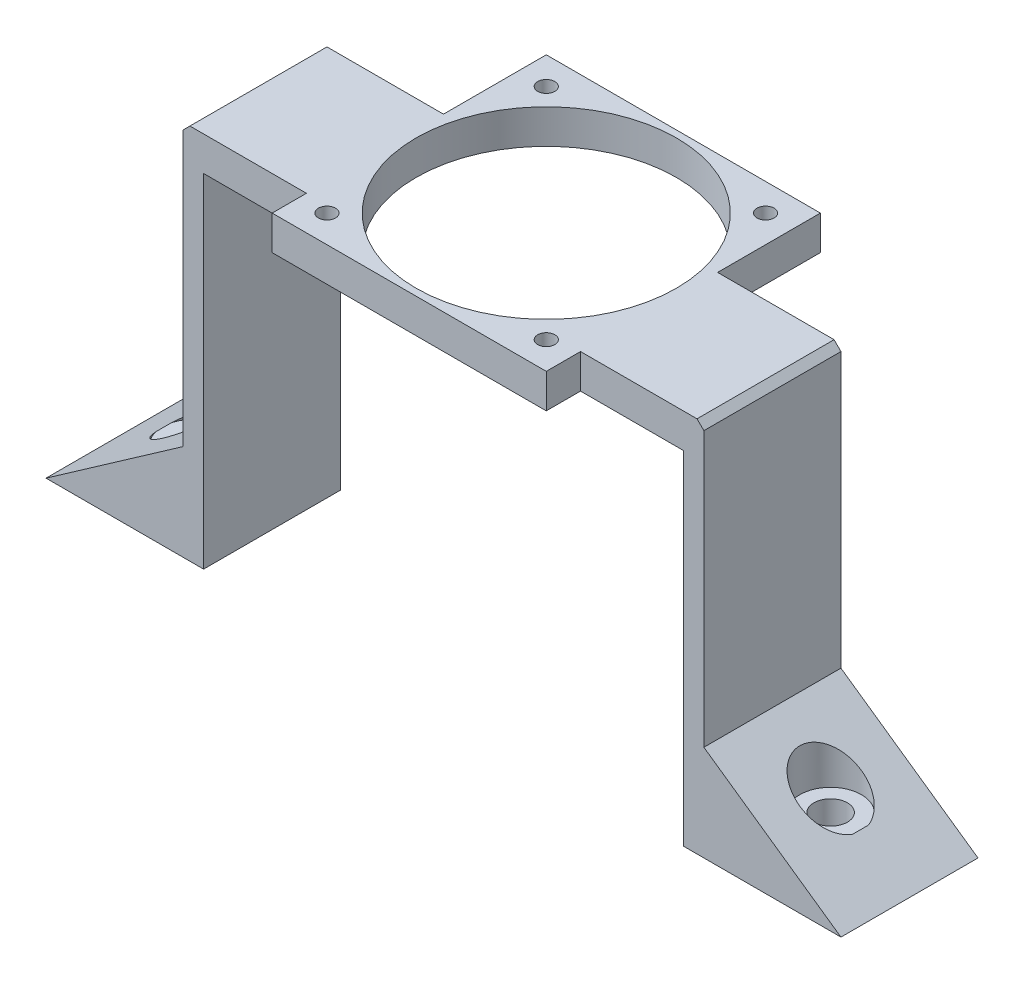
SolidWorks part; units mm, degrees
ref_plane "前视基准面" through (0, 0, 0) normal (0, 0, 1) x (1, 0, 0)
ref_plane "上视基准面" through (0, 0, 0) normal (0, 1, 0) x (1, 0, 0)
ref_plane "右视基准面" through (0, 0, 0) normal (1, 0, 0) x (0, 0, -1)
sketch "草图1" plane through (0, 0, 0) normal (0, 0, 1) x (1, 0, 0)
  line L0 (-33.5856, 27.9887) -> (-33.5856, -25.0113)
  line L1 (-30.5856, 24.9887) -> (39.4144, 24.9887)
  line L2 (-30.5856, 24.9887) -> (-30.5856, -25.0113)
  line L4 (39.4144, 24.9887) -> (39.4144, -25.0113)
  line L5 (-33.5856, 27.9887) -> (42.4144, 27.9887)
  line L6 (42.4144, 27.9887) -> (42.4144, -25.0113)
  line L7 (-30.5856, -25.0113) -> (-33.5856, -25.0113)
  line L8 (39.4144, -25.0113) -> (42.4144, -25.0113)
  dimension "D1" = 70
  dimension "D2" = 50
  dimension "D3" = 3
  dimension "D4" = 3
  dimension "D5" = 3
extrude "凸台-拉伸1" add sketch "草图1" along normal blind 20
sketch "草图2" plane through (0, 27.9887, 0) normal (0, 1, 0) x (1, 0, 0)
  line L1 (42.4144, 0) -> (-33.5856, 0) construction
  line L2 (42.4144, -20) -> (-33.5856, -20) construction
  line L3 (24.4144, -25) -> (24.4144, 15)
  line L4 (-15.5856, -25) -> (-15.5856, 15)
  line L5 (24.4144, 15) -> (-15.5856, 15)
  line L6 (24.4144, -25) -> (-15.5856, -25)
  dimension "D3" = 15
  dimension "D4" = 5
extrude "凸台-拉伸3" add sketch "草图2" against normal blind 3
sketch "草图3" plane through (0, 27.9887, 0) normal (0, 1, 0) x (1, 0, 0)
  circle A0 centre (4.4144, -5) radius 19
  dimension "D2" = 38
extrude "切除-拉伸1" cut sketch "草图3" against normal blind 3
sketch "草图4" plane through (0, 27.9887, 0) normal (0, 1, 0) x (1, 0, 0)
  circle A0 centre (20.4144, 11) radius 1.25
  circle A1 centre (20.4144, -21) radius 1.25
  circle A2 centre (-11.5856, -21) radius 1.25
  circle A3 centre (-11.5856, 11) radius 1.25
  dimension "D5" = 2.5
  dimension "D6" = 2.5
  dimension "D7" = 2.5
  dimension "D8" = 2.5
extrude "切除-拉伸2" cut sketch "草图4" against normal blind 3
sketch "草图5" plane through (0, 27.9887, 0) normal (0, 1, 0) x (1, 0, 0)
  line L12 (-33.5856, -20) -> (-15.5856, -20)
  line L13 (-15.5856, -20) -> (-15.5856, -25)
  line L14 (-15.5856, -25) -> (24.4144, -25)
  line L15 (24.4144, -25) -> (24.4144, -20)
  line L16 (24.4144, -20) -> (42.4144, -20)
  line L17 (42.4144, -20) -> (42.4144, 0)
  line L18 (42.4144, 0) -> (24.4144, 0)
  line L19 (24.4144, 0) -> (24.4144, 15)
  line L20 (24.4144, 15) -> (-15.5856, 15)
  line L21 (-15.5856, 15) -> (-15.5856, 0)
  line L22 (-15.5856, 0) -> (-33.5856, 0)
  line L23 (-33.5856, 0) -> (-33.5856, -20)
  line L24 (-33.5856, -20) -> (-15.5856, -20)
  line L25 (-15.5856, -20) -> (-15.5856, -25)
  line L26 (-15.5856, -25) -> (24.4144, -25)
  line L27 (24.4144, -25) -> (24.4144, -20)
  line L28 (24.4144, -20) -> (42.4144, -20)
  line L29 (42.4144, -20) -> (42.4144, 0)
  line L30 (42.4144, 0) -> (24.4144, 0)
  line L31 (24.4144, 0) -> (24.4144, 15)
  line L32 (24.4144, 15) -> (-15.5856, 15)
  line L33 (-15.5856, 15) -> (-15.5856, 0)
  line L34 (-15.5856, 0) -> (-33.5856, 0)
  line L35 (-33.5856, 0) -> (-33.5856, -20)
  circle A0 centre (4.4144, -5) radius 19 construction
  circle A1 centre (4.4144, -5) radius 19
  dimension "D1" = 0
extrude "凸台-拉伸4" add sketch "草图5" along normal blind 2 contours L24 L25 L26 L27 L28 L29 L30 L31 L32 L33 L34 L35 | A1
sketch "草图6" plane through (0, 27.9887, 0) normal (0, -1, 0) x (1, 0, 0)
  circle A1 centre (20.4144, 21) radius 1.25
  circle A2 centre (20.4144, 21) radius 1.25
  circle A3 centre (20.4144, -11) radius 1.25
  circle A4 centre (20.4144, -11) radius 1.25
  circle A5 centre (-11.5856, -11) radius 1.25
  circle A6 centre (-11.5856, -11) radius 1.25
  circle A7 centre (-11.5856, 21) radius 1.25
  circle A8 centre (-11.5856, 21) radius 1.25
  dimension "D1" = 0
  dimension "D2" = 0
  dimension "D3" = 0
  dimension "D4" = 0
extrude "切除-拉伸3" cut sketch "草图6" against normal blind 2
sketch "草图7" plane through (0, 0, 0) normal (0, 0, -1) x (-1, 0, 0)
  line L0 (33.5856, -25.0113) -> (53.5856, -25.0113)
  line L1 (53.5856, -25.0113) -> (33.5856, -11.0218)
  line L2 (33.5856, 29.9887) -> (33.5856, -25.0113) construction
  line L3 (33.5856, -11.0218) -> (33.5856, -25.0113)
  dimension "D1" = 20
extrude "凸台-拉伸5" add sketch "草图7" against normal blind 20
sketch "草图9" plane through (0, 0, -15) normal (0, 0, -1) x (-1, 0, 0)
  line L0 (-4.4144, 29.9887) -> (-4.4144, 24.9887)
  line L1 (-24.4144, 29.9887) -> (15.5856, 29.9887) construction
  line L2 (-24.4144, 24.9887) -> (15.5856, 24.9887) construction
  point P6 (-4.4144, 24.9887)
  point P7 (0, 0)
sketch "草图10" plane through (0, 0, -15) normal (0, 0, -1) x (-1, 0, 0)
  line L0 (-4.4144, 24.9887) -> (-4.4144, -56.6503)
  line L1 (-4.4144, -56.6503) -> (-57.4894, -56.6503)
  line L2 (-57.4894, -56.6503) -> (-57.4894, 45.6644)
  line L3 (-57.4894, 45.6644) -> (-4.4144, 45.6644)
  line L4 (-4.4144, 45.6644) -> (-4.4144, 24.9887)
extrude "切除-拉伸4" cut sketch "草图10" against normal blind 59
sketch "草图11" plane through (0, -25.0113, 0) normal (0, -1, 0) x (1, 0, 0)
  circle A0 centre (-42.0856, 10) radius 2.45
  dimension "D1" = 4.9
extrude "切除-拉伸5" cut sketch "草图11" against normal blind 59
ref_plane "基准面1" through (0, -20.0113, 0) normal (0, -1, 0) x (-1, 0, 0)
sketch "草图12" plane through (0, -20.0113, 0) normal (0, -1, 0) x (-1, 0, 0)
  circle A0 centre (42.0856, -10) radius 4.5
  dimension "D1" = 9
extrude "切除-拉伸6" cut sketch "草图12" against normal blind 59
mirror "镜向2" about plane through (4.4144, 24.9887, 44) normal (-1, 0, 0) of bodies 117
chamfer "倒角1" distance 1 angle 45 2 edges at (42.4144, 29.9887, 10) (-33.5856, 29.9887, 10)
